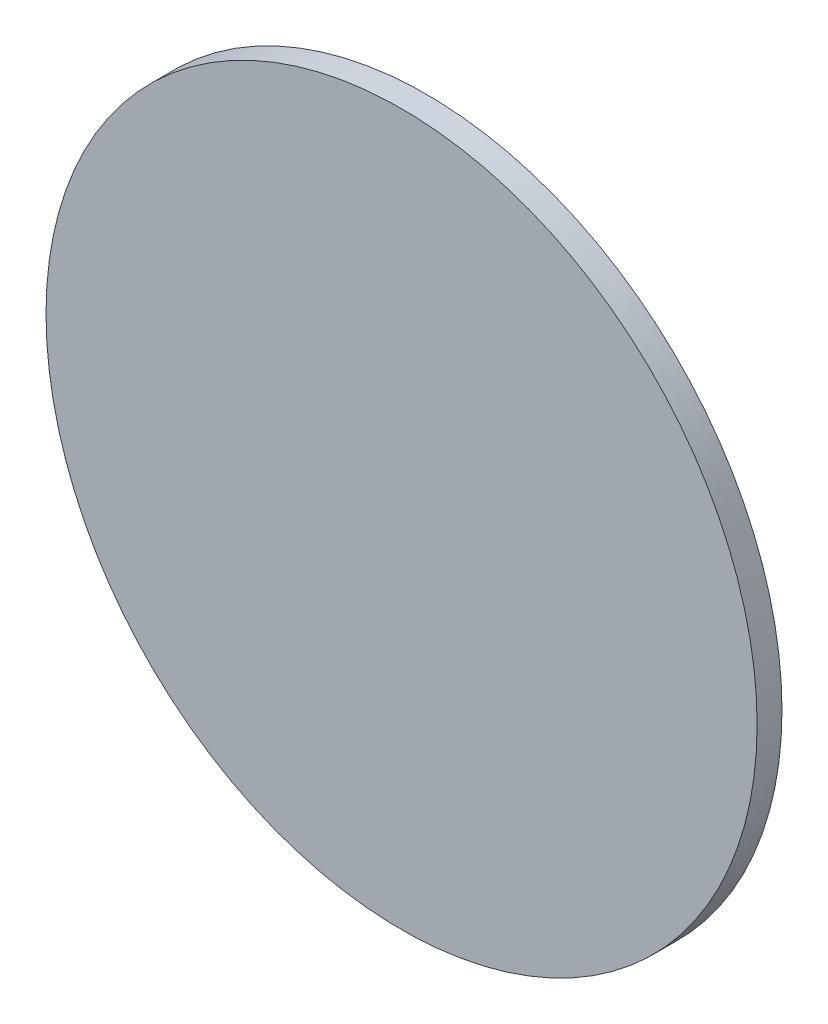
SolidWorks part; units mm, degrees
ref_plane "Plan de face" through (0, 0, 0) normal (0, 0, 1) x (1, 0, 0)
ref_plane "Plan de dessus" through (0, 0, 0) normal (0, 1, 0) x (1, 0, 0)
ref_plane "Plan de droite" through (0, 0, 0) normal (1, 0, 0) x (0, 0, -1)
sketch "Esquisse1" plane through (0, 0, 0) normal (0, 0, 1) x (1, 0, 0)
  circle A0 centre (0, 0) radius 143
  dimension "D1" = 286
extrude "Boss.-Extru.1" add sketch "Esquisse1" along normal blind 10
sketch "Esquisse2" plane through (0, 0, 0) normal (0, 0, -1) x (-1, 0, 0)
  line L1 (-143, 37.25) -> (-123, 37.25)
  line L2 (-143, 37.25) -> (-143, -37.25)
  line L3 (-143, -37.25) -> (-123, -37.25)
  line L4 (-123, 37.25) -> (-123, -37.25)
  line L5 (123, 37.25) -> (143, 37.25)
  line L6 (123, 37.25) -> (123, -37.25)
  line L7 (123, -37.25) -> (143, -37.25)
  line L8 (143, 37.25) -> (143, -37.25)
  line L9 (25, 25) -> (-25, 25)
  line L10 (25, 25) -> (25, -25)
  line L11 (25, -25) -> (-25, -25)
  line L12 (-25, 25) -> (-25, -25)
  circle A0 centre (32, 48) radius 1.65
  circle A2 centre (-64, -32) radius 1.65
  circle A3 centre (0, -32) radius 1.65
  circle A4 centre (-16, -32) radius 1.65
  circle A5 centre (0, 32) radius 1.65
  circle A6 centre (0, 64) radius 1.65
  circle A7 centre (0, 48) radius 1.65
  circle A8 centre (0, -48) radius 1.65
  circle A10 centre (0, -64) radius 1.65
  circle A11 centre (-16, 32) radius 1.65
  circle A12 centre (-16, 64) radius 1.65
  circle A13 centre (-16, 48) radius 1.65
  circle A14 centre (-32, 64) radius 1.65
  circle A15 centre (16, 64) radius 1.65
  circle A16 centre (16, 48) radius 1.65
  circle A17 centre (-32, 48) radius 1.65
  circle A18 centre (16, 32) radius 1.65
  circle A19 centre (-32, 32) radius 1.65
  circle A20 centre (-48, 48) radius 1.65
  circle A21 centre (32, 32) radius 1.65
  circle A22 centre (-64, 32) radius 1.65
  circle A23 centre (-32, -32) radius 1.65
  circle A24 centre (-64, 48) radius 1.65
  circle A25 centre (-48, 32) radius 1.65
  circle A26 centre (-48, 64) radius 1.65
  circle A27 centre (-64, 64) radius 1.65
  circle A28 centre (32, 64) radius 1.65
  circle A29 centre (-48, -32) radius 1.65
  circle A30 centre (64, -32) radius 1.65
  circle A31 centre (16, -48) radius 1.65
  circle A32 centre (16, -64) radius 1.65
  circle A33 centre (64, -64) radius 1.65
  circle A34 centre (48, -64) radius 1.65
  circle A35 centre (64, -48) radius 1.65
  circle A36 centre (48, -48) radius 1.65
  circle A37 centre (48, -32) radius 1.65
  circle A38 centre (16, -32) radius 1.65
  circle A39 centre (32, -64) radius 1.65
  circle A40 centre (32, -32) radius 1.65
  circle A41 centre (32, -48) radius 1.65
  circle A42 centre (-48, -48) radius 1.65
  circle A43 centre (48, 48) radius 1.65
  circle A44 centre (-32, -64) radius 1.65
  circle A45 centre (-48, -64) radius 1.65
  circle A46 centre (64, 64) radius 1.65
  circle A47 centre (64, 32) radius 1.65
  circle A48 centre (48, 64) radius 1.65
  circle A49 centre (-16, -64) radius 1.65
  circle A50 centre (-16, -48) radius 1.65
  circle A51 centre (48, 32) radius 1.65
  circle A52 centre (-32, -48) radius 1.65
  circle A53 centre (64, 48) radius 1.65
  circle A54 centre (-64, 16) radius 1.65
  circle A55 centre (48, 0) radius 1.65
  circle A56 centre (-48, 0) radius 1.65
  circle A57 centre (-64, -16) radius 1.65
  circle A58 centre (48, -16) radius 1.65
  circle A59 centre (-48, -16) radius 1.65
  circle A60 centre (64, 16) radius 1.65
  circle A61 centre (-48, 16) radius 1.65
  circle A62 centre (-64, -64) radius 1.65
  circle A63 centre (48, 16) radius 1.65
  circle A64 centre (-64, -48) radius 1.65
  circle A65 centre (-64, 0) radius 1.65
  circle A67 centre (32, 0) radius 1.65
  circle A68 centre (32, -16) radius 1.65
  circle A73 centre (32, 16) radius 1.65
  circle A74 centre (64, -16) radius 1.65
  circle A76 centre (64, 0) radius 1.65
  circle A98 centre (-96, -64) radius 1.65
  circle A99 centre (-96, -48) radius 1.65
  circle A100 centre (-96, -32) radius 1.65
  circle A101 centre (-96, -16) radius 1.65
  circle A102 centre (-96, 0) radius 1.65
  circle A103 centre (-96, 16) radius 1.65
  circle A104 centre (-96, 32) radius 1.65
  circle A105 centre (-96, 48) radius 1.65
  circle A106 centre (-96, 64) radius 1.65
  circle A107 centre (-112, -64) radius 1.65
  circle A108 centre (-112, -48) radius 1.65
  circle A109 centre (-112, -32) radius 1.65
  circle A110 centre (-112, -16) radius 1.65
  circle A111 centre (-112, 0) radius 1.65
  circle A112 centre (-112, 16) radius 1.65
  circle A113 centre (-112, 32) radius 1.65
  circle A114 centre (-112, 48) radius 1.65
  circle A115 centre (-112, 64) radius 1.65
  circle A116 centre (-64, 96) radius 1.65
  circle A117 centre (-48, 96) radius 1.65
  circle A118 centre (-32, 96) radius 1.65
  circle A119 centre (-16, 96) radius 1.65
  circle A120 centre (0, 96) radius 1.65
  circle A121 centre (16, 96) radius 1.65
  circle A122 centre (32, 96) radius 1.65
  circle A123 centre (48, 96) radius 1.65
  circle A124 centre (64, 96) radius 1.65
  circle A125 centre (64, 112) radius 1.65
  circle A126 centre (48, 112) radius 1.65
  circle A127 centre (32, 112) radius 1.65
  circle A128 centre (16, 112) radius 1.65
  circle A129 centre (0, 112) radius 1.65
  circle A130 centre (-16, 112) radius 1.65
  circle A131 centre (-32, 112) radius 1.65
  circle A132 centre (-48, 112) radius 1.65
  circle A133 centre (-64, 112) radius 1.65
  circle A135 centre (96, 0) radius 1.65
  circle A136 centre (96, 16) radius 1.65
  circle A137 centre (96, 32) radius 1.65
  circle A138 centre (96, 48) radius 1.65
  circle A139 centre (96, 64) radius 1.65
  circle A140 centre (96, -16) radius 1.65
  circle A141 centre (96, -32) radius 1.65
  circle A142 centre (96, -48) radius 1.65
  circle A143 centre (96, -64) radius 1.65
  circle A144 centre (112, -64) radius 1.65
  circle A145 centre (112, -48) radius 1.65
  circle A146 centre (112, -32) radius 1.65
  circle A147 centre (112, -16) radius 1.65
  circle A148 centre (112, 0) radius 1.65
  circle A149 centre (112, 16) radius 1.65
  circle A150 centre (112, 32) radius 1.65
  circle A151 centre (112, 48) radius 1.65
  circle A152 centre (112, 64) radius 1.65
  circle A153 centre (0, 128) radius 1.65
  circle A154 centre (16, 128) radius 1.65
  circle A155 centre (32, 128) radius 1.65
  circle A156 centre (-16, 128) radius 1.65
  circle A157 centre (-32, 128) radius 1.65
  circle A160 centre (-96, 80) radius 1.65
  circle A161 centre (-80, 96) radius 1.65
  circle A162 centre (96, 80) radius 1.65
  circle A163 centre (80, 96) radius 1.65
  circle A164 centre (0, -96) radius 1.65
  circle A165 centre (0, -112) radius 1.65
  circle A166 centre (0, -128) radius 1.65
  circle A167 centre (16, -96) radius 1.65
  circle A168 centre (32, -96) radius 1.65
  circle A169 centre (48, -96) radius 1.65
  circle A170 centre (64, -96) radius 1.65
  circle A171 centre (16, -112) radius 1.65
  circle A172 centre (32, -112) radius 1.65
  circle A173 centre (48, -112) radius 1.65
  circle A174 centre (64, -112) radius 1.65
  circle A175 centre (16, -128) radius 1.65
  circle A176 centre (-48, -112) radius 1.65
  circle A177 centre (32, -128) radius 1.65
  circle A178 centre (-16, -96) radius 1.65
  circle A179 centre (-16, -112) radius 1.65
  circle A180 centre (-16, -128) radius 1.65
  circle A181 centre (-32, -96) radius 1.65
  circle A182 centre (-32, -112) radius 1.65
  circle A183 centre (-32, -128) radius 1.65
  circle A184 centre (-48, -96) radius 1.65
  circle A185 centre (-64, -112) radius 1.65
  circle A186 centre (-64, -96) radius 1.65
  circle A187 centre (-80, -96) radius 1.65
  circle A188 centre (80, -96) radius 1.65
  circle A192 centre (96, -80) radius 1.65
  circle A193 centre (-96, -80) radius 1.65
  point P14 (0, 0)
  point P15 (0, 0)
  point P18 (0, 0)
  point P19 (0, 0)
  point P20 (-16, -19.3)
  point P23 (-16, 19.3)
  point P28 (0, 0)
  point P29 (-16, -16)
  point P30 (16, -16)
  point P31 (16, 16)
  point P32 (-16, 16)
  point P33 (0, 0)
  point P36 (0, 0)
  point P37 (38.0111, 16)
  point P38 (55.8996, 16)
  point P39 (74.6314, 16)
  point P40 (-37.269, 16)
  point P41 (-56.3928, 16)
  point P44 (-73.8956, 16)
  point P45 (32, 0)
  point P52 (32, -16)
  point P53 (-37.269, 16)
  point P54 (48, -16)
  point P67 (16, -31.0265)
  point P68 (16, -46.6093)
  point P69 (16, -64.0858)
  point P70 (74.6314, 16)
  point P71 (74.6314, -16)
  point P72 (0, 0)
  point P97 (64, 0)
  point P98 (64, -16)
  point P99 (-32, 16)
  point P100 (-16, 32)
  point P101 (-32, 32)
  point P102 (16, 32)
  point P103 (32, 32)
  point P104 (48, 32)
  point P105 (64, 32)
  point P106 (-48, 16)
  point P107 (-48, 32)
  point P108 (-32, -16)
  point P109 (-16, -32)
  point P110 (-16, -48)
  point P111 (-16, -64)
  point P136 (-32, -32)
  point P137 (-32, -48)
  point P138 (-32, -64)
  point P139 (-46.0504, -16)
  point P140 (-48, -16)
  point P141 (-48, -32)
  point P142 (-48, -48)
  point P143 (-48, -64)
  point P144 (-64, 16)
  point P145 (-64, 32)
  point P146 (-64, -16)
  point P147 (-64, -32)
  point P172 (-64, -48)
  point P173 (-64, -64)
  point P174 (32, -31.0265)
  point P175 (32, -46.6093)
  point P176 (32, -64.0858)
  point P177 (16, -46.6093)
  point P178 (32, -48)
  point P179 (48, -31.0265)
  point P180 (64, -31.0265)
  point P181 (48, -48)
  point P182 (64, -48)
  point P183 (48, -64.0858)
  point P184 (64, -64.0858)
  point P209 (64, 48)
  point P210 (64, 64)
  point P211 (48, 48)
  point P212 (32, 48)
  point P213 (16, 48)
  point P214 (16, 64)
  point P215 (32, 64)
  point P216 (48, 64)
  point P217 (-16, 48)
  point P218 (-16, 64)
  point P219 (-32, 48)
  point P220 (-32, 64)
  point P221 (-48, 48)
  point P222 (-48, 64)
  point P227 (-64, 48)
  point P228 (-64, 64)
  point P229 (0, 0)
  point P230 (0, 0)
  point P231 (0, 0)
  point P232 (0, 0)
  point P233 (0, 0)
  point P234 (86.1597, -90.4882)
  point P239 (-153.3852, -0.176)
  point P240 (0, 0)
  point P243 (0, 0)
  point P244 (0, 0)
  point P247 (-91.6394, -64)
  point P248 (-91.433, -64)
  point P251 (-91.433, -48)
  point P254 (-91.433, -32)
  point P257 (-91.433, -16)
  point P262 (-91.433, 0)
  point P265 (-91.433, 16)
  point P268 (-91.433, 32)
  point P271 (-91.433, 48)
  point P278 (-91.433, 64)
  point P281 (-108.3856, -64)
  point P284 (-108.3856, -48)
  point P287 (-108.3856, -32)
  point P290 (-108.3856, -16)
  point P293 (-108.3856, 0)
  point P296 (-108.3856, 16)
  point P299 (-108.3856, 32)
  point P302 (-108.3856, 48)
  point P303 (0, 0)
  point P306 (105.5005, 7.5628)
  point P311 (-108.3856, 64)
  point P321 (-64, 84.216)
  point P324 (-64, 94.6761)
  point P327 (0, 0)
  point P332 (-48, 96)
  point P335 (-32, 96)
  point P338 (-16, 96)
  point P341 (0, 96)
  point P344 (16, 96)
  point P347 (32, 96)
  point P350 (0, 0)
  point P351 (48, 96)
  point P354 (64, 96)
  point P357 (64, 112.294)
  point P360 (48, 112)
  point P363 (32, 112)
  point P366 (16, 112)
  point P369 (0, 112)
  point P372 (-16, 112)
  point P375 (-32, 112)
  point P378 (-48, 112)
  point P381 (-64, 112)
  point P382 (0, 0)
  point P383 (0, 0)
  point P386 (91.0271, 64)
  point P389 (91.0271, -31.0265)
  point P390 (91.0271, 0)
  point P391 (0, 0)
  point P392 (0, 0)
  point P395 (96, 16)
  point P398 (96, 32)
  point P401 (96, 48)
  point P404 (96, 64)
  point P405 (96, -16)
  point P408 (96, -31.0265)
  point P411 (96, -48)
  point P414 (96, -64.0858)
  point P415 (0, 0)
  point P416 (0, 0)
  point P417 (106.0456, 15.2868)
  point P418 (0, 0)
  point P419 (0, 0)
  point P420 (0, 0)
  point P421 (0, 0)
  point P422 (0, 0)
  point P423 (16, -32)
  point P424 (16, -64)
  point P425 (48, -64)
  point P426 (96, -56.9435)
  point P427 (96, -64)
  point P430 (176.8569, -84.5035)
  point P431 (113.7905, -64)
  point P432 (0, 0)
  point P433 (0, 0)
  point P436 (112, -48)
  point P439 (112, -32)
  point P442 (112, -16)
  point P445 (112, 0)
  point P448 (112, 16)
  point P451 (112, 32)
  point P454 (112, 48)
  point P457 (112, 64)
  point P458 (-96, 16)
  point P459 (-96, 32)
  point P460 (-96, 48)
  point P461 (-96, 64)
  point P462 (-96, -32)
  point P463 (-96, -48)
  point P464 (-96, -64)
  point P465 (0, 0)
  point P466 (0, 0)
  point P467 (0, 0)
  point P468 (0, 0)
  point P469 (0, 0)
  point P470 (-112, -48)
  point P471 (-112, -32)
  point P472 (-112, -16)
  point P473 (-112, 0)
  point P474 (-112, 16)
  point P475 (-112, 32)
  point P476 (-112, 48)
  point P477 (-112, 64)
  point P480 (48, 128.3621)
  point P481 (0, 128.6637)
  point P484 (16, 128)
  point P487 (32, 128)
  point P490 (-16, 128)
  point P491 (0, 0)
  point P492 (0, 0)
  point P495 (-32, 128)
  point P498 (-79.8893, 64)
  point P499 (0, 0)
  point P500 (0, 0)
  point P503 (-80, 79.1435)
  point P506 (-96, 80)
  point P507 (-80, 96)
  point P508 (96, 80)
  point P511 (81.8903, 96)
  point P514 (0, -97.9102)
  point P517 (0, -110.2684)
  point P520 (0, -126.548)
  point P521 (0, -127.9348)
  point P524 (16, -96)
  point P527 (32, -96)
  point P530 (48, -96)
  point P533 (64, -96)
  point P536 (16, -112)
  point P539 (32, -112)
  point P542 (0, 0)
  point P545 (48, -112)
  point P548 (64, -112)
  point P551 (16, -128)
  point P554 (0, 0)
  point P555 (32, -128)
  point P558 (-16, -96)
  point P561 (-16, -112)
  point P564 (-16, -128)
  point P567 (-32, -96)
  point P570 (-32, -112)
  point P573 (-32, -128)
  point P576 (-48, -112)
  point P577 (-48, -96)
  point P580 (-64, -112)
  point P583 (-64, -96)
  point P586 (-194.5683, 80)
  point P587 (-80, -96)
  point P590 (80, -96)
  point P593 (-96, -81.2509)
  point P594 (96, -81.9644)
  point P595 (0, 0)
  point P596 (0, 0)
  point P597 (80, -64)
  point P600 (80, -79.6591)
  point P601 (0, 0)
  point P602 (0, 0)
  point P605 (149.0951, -101.9957)
  point P606 (96, -80)
  point P607 (0, 0)
  point P608 (0, 0)
  point P609 (0, 0)
  point P610 (-96, -80)
  point P611 (0, 0)
  dimension "D7" = 25
  dimension "D9" = 25
  dimension "D12" = 12.25
  dimension "D5" = 12.25
  dimension "D17" = 32
  dimension "D29" = 32
  dimension "D2" = 20
  dimension "D3" = 98
  dimension "D4" = 20
  dimension "D6" = 98
  dimension "D8" = 25
  dimension "D10" = 25
  dimension "D11" = 25
  dimension "D13" = 12.25
  dimension "D14" = 12.25
  dimension "D21" = 16
  dimension "D23" = 32
  dimension "D26" = 32
